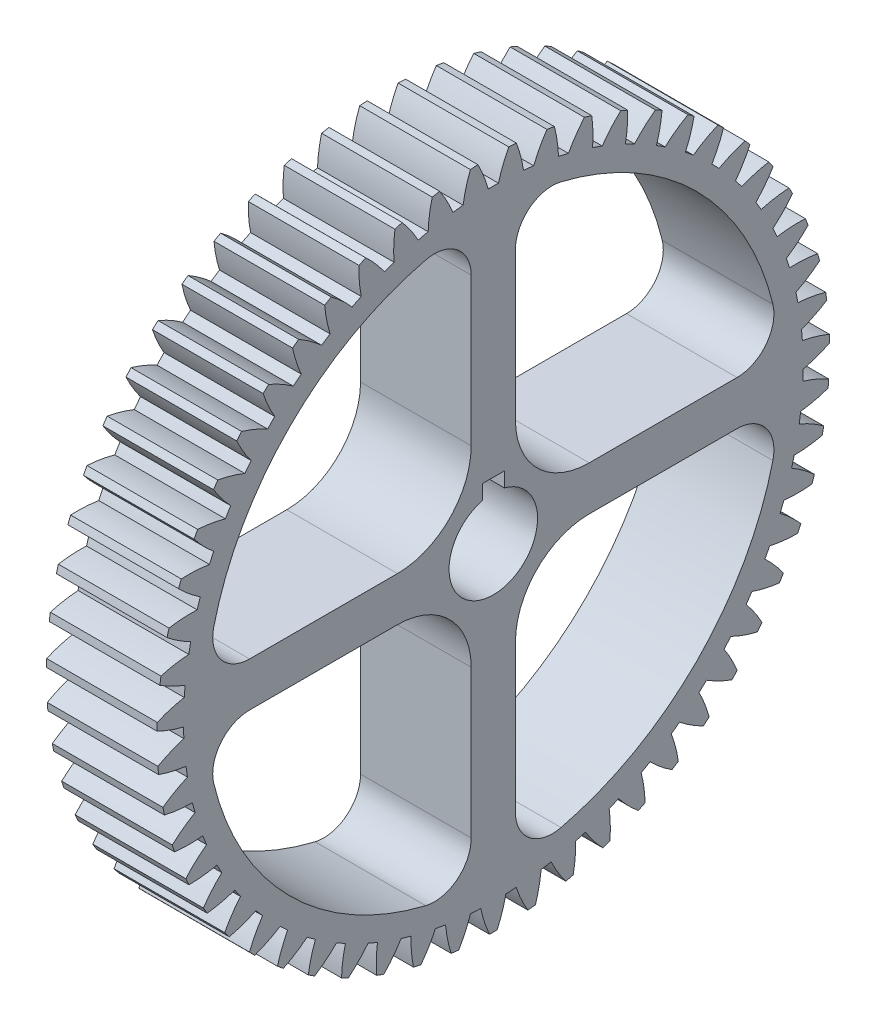
SolidWorks part; units mm, degrees
ref_plane "Plane1" through (0, 0, 0) normal (0, 0, 1) x (1, 0, 0)
ref_plane "Plane2" through (0, 0, 0) normal (0, 1, 0) x (1, 0, 0)
ref_plane "Plane3" through (0, 0, 0) normal (1, 0, 0) x (0, 0, -1)
other "Configuration Table"
sketch "HoldingSke" plane through (0, 0, 0) normal (0, 1, 0) x (1, 0, 0)
  line L0 (0, 0) -> (0.717, -1.0239)
  line L1 (-15, 0) -> (100, 0) construction
  line L2 (0, 0) -> (-2.1039, 2.3779)
  line L3 (0, 0) -> (-11.863, 4.5341)
  line L4 (0, 0) -> (4.9534, 7.0742)
  line L5 (0, 0) -> (-46.8476, -17.4728)
  line L6 (0, 0) -> (-6.2172, -4.1948)
  line L7 (-2.1039, 2.3779) -> (8.6586, 51.2059)
  line L8 (-76.2, 54.61) -> (-76.1, 54.61)
  line L9 (-71.009, 38.7566) -> (-53.1078, 45.2721)
  line L10 (-76.2, 71.12) -> (104.1128, 71.12)
  line L11 (0, 0) -> (-7.5, 0)
  line L12 (-76.2, 101.6) -> (-76.17, 101.6)
  line L13 (24.9733, 27.94) -> (52.9518, 28.4284)
  line L14 (24.9733, 27.94) -> (24.9743, 27.94)
  line L15 (24.9733, 27.94) -> (100.4006, 29.5858)
  line L16 (-63.627, -0.8) -> (-12.827, -0.8)
  circle A0 centre (0, 0) radius 0.4
  circle A1 centre (0, 0) radius 20.999
  circle A2 centre (0, 0) radius 37.5
  circle A3 centre (0, 0) radius 0.4
  dimension "MHD" = 41.998
  dimension "Hub_dia" = 75
  dimension "Bore" = 0.8
  dimension "MBD" = 0.8
  dimension "Num_teeth" = 55
  dimension "Pitch" = 1.25
  dimension "Overall_len" = 50
  dimension "Show_teeth" = 55
  dimension "Thickness" = 7.5
  dimension "OAL" = 50.0001
  dimension "T_dim" = 0.1
  dimension "Ap" = 20
  dimension "H" = 19.05
  dimension "Pitch_radius" = 180.3128
  dimension "Width" = 7.5
  dimension "Backlash" = 0.03
  dimension "Addendum_fac" = 1
  dimension "Dedendum_fac" = 1.25
  dimension "Clearance_fac" = 0.25
  dimension "Dedendum_add" = 0.001
  dimension "Module" = 0.8
sketch "BasProSke" plane through (0, 0, 0) normal (0, 1, 0) x (1, 0, 0)
  line L0 (-10, 0) -> (60, 0) construction
  line L1 (0, 0) -> (0, 22.8)
  line L2 (0, 0) -> (7.5, 0)
  line L3 (7.5, 0) -> (7.5, 22.8)
  line L4 (7.5, 22.8) -> (0, 22.8)
  dimension "Thickness" = 7.5
  dimension "Diameter" = 45.6
revolve "Base-Revolve" add sketch "BasProSke" angle 360 about L0
sketch "TooCutSke" plane through (0, 0, 0) normal (1, 0, 0) x (0, 0, -1)
  line L1 (0, 0) -> (0, 107) construction
  line L2 (0, 0) -> (-0.6807, 21.9895) construction
  line L3 (0, 0) -> (-2.511, 43.9132) construction
  line L4 (-0.6807, 21.9895) -> (-1.2555, 21.9566) construction
  arc A0 (0.3461, 20.9961) -> (-0.3461, 20.9961) centre (0, 0) ccw
  arc A1 (1.0581, 22.8009) -> (-1.0581, 22.8009) centre (0, 0) ccw
  circle A2 centre (0, 0) radius 22 construction
  circle A3 centre (0, 0) radius 20.6732 construction
  arc A4 (-0.3461, 20.9961) -> (-1.0581, 22.8009) centre (-8.8382, 18.6887) ccw
  arc A5 (1.0581, 22.8009) -> (0.3461, 20.9961) centre (8.8382, 18.6887) ccw
  dimension "Root_dia" = 41.998
  dimension "Overcut_dia" = 45.6508
  dimension "Pitch_dia" = 44
  dimension "Base_dia" = 41.3465
  dimension "Flank_rad" = 8.8
  dimension "Half_ang" = 3.273
  dimension "Half_CT" = 0.5757
extrude "ToothCut" cut sketch "TooCutSke" along normal through all
fillet "Breaks" [suppressed] radius 0.016
fillet "RootFillets" [suppressed] radius 0.201
pattern_circular "TeethCuts" count 55 every 6.545 about axis through (-10, 0, 0) along (1, 0, 0) of "ToothCut", "RootFillets", "Breaks"
sketch "HubNeaOneSke" plane through (0, 0, 0) normal (-1, 0, 0) x (0, 0, 1)
  circle A0 centre (0, 0) radius 20.999
  dimension "Diameter" = 41.998
extrude "HubNearOne" [suppressed] add sketch "HubNeaOneSke" along normal blind 42.5001
sketch "HubNeaBotSke" plane through (0, 0, 0) normal (-1, 0, 0) x (0, 0, 1)
  circle A0 centre (0, 0) radius 20.999
  dimension "Diameter" = 41.998
extrude "HubNearBoth" [suppressed] add sketch "HubNeaBotSke" along normal blind 21.25
ref_plane "FarPln" through (7.5, 0, 0) normal (1, 0, 0) x (0, 0, -1)
sketch "HubFarSke" plane through (7.5, 0, 0) normal (1, 0, 0) x (0, 0, -1)
  circle A0 centre (0, 0) radius 20.999
  dimension "Diameter" = 41.998
extrude "HubFar" [suppressed] add sketch "HubFarSke" along normal blind 21.25
sketch "BorSke" plane through (0, 0, 0) normal (1, 0, 0) x (0, 0, -1)
  circle A0 centre (0, 0) radius 0.4
  dimension "Diameter" = 0.8
extrude "Bore" cut sketch "BorSke" along normal mid plane 100.0001
sketch "KeySke" plane through (0, 0, 0) normal (1, 0, 0) x (0, 0, -1)
  line L0 (-0.05, 0) -> (-0.05, 0.5)
  line L1 (-0.05, 0.5) -> (0.05, 0.5)
  line L2 (0.05, 0.5) -> (0.05, 0)
  line L3 (0, 0) -> (0, 34) construction
  line L4 (-0.05, 0) -> (0.05, 0)
  dimension "Offset" = 0.5
  dimension "Width" = 0.1
extrude "Keyway" [suppressed] cut sketch "KeySke" along normal mid plane 100.0001
pattern_circular "Keyway2" [suppressed] count 2 every 90 about axis through (-10, 0, 0) along (1, 0, 0)
sketch "Sketch1" plane through (7.5, 0, 0) normal (1, 0, 0) x (0, 0, -1)
  circle A0 centre (0, 0) radius 0.4 construction
  circle A1 centre (0, 0) radius 0.4
extrude "Boss-Extrude1" add sketch "Sketch1" against normal up to surface (7.5 mm away) up to face at (0, 0, -0.4)
sketch "Sketch2" plane through (7.5, 0, 0) normal (1, 0, 0) x (0, 0, -1)
  line L0 (-15.0591, 14.635) -> (-13.9834, 13.5896) construction
  circle A0 centre (0, 0) radius 19.499
  arc A1 (-14.8158, 14.8812) -> (-15.2982, 14.3848) centre (0, 0) ccw construction
  dimension "D1" = 1.5
extrude "Cut-Extrude1" cut sketch "Sketch2" against normal blind 10
sketch "Sketch3" plane through (7.5, 0, 0) normal (1, 0, 0) x (0, 0, -1)
  line L0 (0, 19.499) -> (0, -19.499) construction
  line L5 (-19.499, 0) -> (19.499, 0) construction
  line L6 (-19.4412, -1.5) -> (-6.5, -1.5)
  line L7 (-19.4412, 1.5) -> (-6.5, 1.5)
  line L8 (-19.499, 1.5) -> (19.499, 1.5) construction
  line L9 (-19.499, -1.5) -> (19.499, -1.5) construction
  line L10 (-1.5, 19.4412) -> (-1.5, 6.5)
  line L11 (1.5, 19.4412) -> (1.5, 6.5)
  line L12 (-1.5, 19.499) -> (-1.5, -19.499) construction
  line L13 (1.5, 19.499) -> (1.5, -19.499) construction
  line L14 (-1.5, -6.5) -> (-1.5, -19.4412)
  line L15 (6.5, 1.5) -> (19.4412, 1.5)
  line L16 (1.5, -6.5) -> (1.5, -19.4412)
  line L17 (6.5, -1.5) -> (19.4412, -1.5)
  circle A0 centre (0, 0) radius 19.499 construction
  arc A1 (19.4412, -1.5) -> (19.4412, 1.5) centre (0, 0) ccw
  arc A2 (-1.5, -19.4412) -> (1.5, -19.4412) centre (0, 0) ccw
  arc A3 (-19.4412, 1.5) -> (-19.4412, -1.5) centre (0, 0) ccw
  arc A4 (1.5, 19.4412) -> (-1.5, 19.4412) centre (0, 0) ccw
  arc A5 (-6.5, 1.5) -> (-1.5, 6.5) centre (-6.5, 6.5) ccw
  arc A6 (1.5, 6.5) -> (6.5, 1.5) centre (6.5, 6.5) ccw
  arc A7 (6.5, -1.5) -> (1.5, -6.5) centre (6.5, -6.5) ccw
  arc A8 (-1.5, -6.5) -> (-6.5, -1.5) centre (-6.5, -6.5) ccw
  point P0 (0, 0)
  point P8 (0, 0)
  point P11 (0, 0)
  point P37 (1.5, -1.5)
  dimension "D5" = 5
  dimension "D1" = 1.5
  dimension "D2" = 1.5
  dimension "D3" = 1.5
  dimension "D4" = 1.5
extrude "Boss-Extrude2" add sketch "Sketch3" against normal up to surface (7.5 mm away)
fillet "Fillet1" radius 2.5 8 edges at (3.75, 1.5, 19.4412) (3.75, -1.5, 19.4412) (3.75, -19.4412, -1.5) (3.75, -19.4412, 1.5) (3.75, 19.4412, 1.5) (3.75, 19.4412, -1.5) (3.75, 1.5, -19.4412) (3.75, -1.5, -19.4412)
sketch "Sketch4" plane through (0, 0, 0) normal (-1, 0, 0) x (0, 0, 1)
  line L0 (0, 0) -> (0, 50000) construction
  line L1 (-0.75, 2.9047) -> (-0.75, 3.9047)
  line L2 (0.75, 2.9047) -> (0.75, 3.9047)
  line L3 (-0.75, 3.9047) -> (0.75, 3.9047)
  arc A0 (-0.75, 2.9047) -> (0.75, 2.9047) centre (0, 0) ccw
  point P7 (-0.75, 3.4047)
  dimension "D1" = 6
  dimension "D2" = 1
  dimension "D3" = 1.5
extrude "Cut-Extrude2" cut sketch "Sketch4" against normal through all
equation "' \"Module@HoldingSke\" = 6.35"
equation "' \"Num_teeth@HoldingSke\" = 12"
equation "' \"Ap@HoldingSke\" =  20"
equation "' \"Ap@HoldingSke\" = 20"
equation "' \"Width@HoldingSke\" = 0.5 * 25.4"
equation "' \"Hub_dia@HoldingSke\"= 1 * 25.4"
equation "' \"Hub_dia@HoldingSke\" = 1 * 25.4"
equation "' \"Overall_len@HoldingSke\" = 1.0 * 25.4"
equation "' \"Bore@HoldingSke\" = 0.75 * 25.4"
equation "' \"T_dim@HoldingSke\" = 0.1 * 25.4"
equation "' \"Width@KeySke\" = 0.25 * 25.4"
equation "' \"Show_teeth@HoldingSke\" = 13"
equation "' \"Backlash@HoldingSke\" = 0.009 * 25.4"
equation "' \"Addendum_fac@HoldingSke\" = 1.0"
equation "' \"Dedendum_fac@HoldingSke\" = 1.25"
equation "' \"Dedendum_add@HoldingSke\" = 0.00005 * 25.4"
equation "' \"Clearance_fac@HoldingSke\" = 0.25"
equation "\"Pitch@HoldingSke\" = 1 / \"Module@HoldingSke\""
equation "\"Overcut_dia@TooCutSke\" = (\"Num_teeth@HoldingSke\" + 2 * \"Addendum_fac@HoldingSke\") / \"Pitch@HoldingSke\" + 0.002 * 25.4"
equation "\"Pitch_dia@TooCutSke\" = \"Num_teeth@HoldingSke\" / \"Pitch@HoldingSke\""
equation "\"Base_dia@TooCutSke\" = \"Num_teeth@HoldingSke\" / \"Pitch@HoldingSke\" * cos((\"Ap@HoldingSke\"  * 3.14159265 / 180))"
equation "\"Root_dia@TooCutSke\" = (\"Num_teeth@HoldingSke\" + 2) / \"Pitch@HoldingSke\" - 2 * (\"Addendum_fac@HoldingSke\" + \"Dedendum_fac@HoldingSke\") / \"Pitch@HoldingSke\" - \"Dedendum_add@HoldingSke\" * 2"
equation "\"Half_ang@TooCutSke\" = 180 / \"Num_teeth@HoldingSke\""
equation "\"Half_CT@TooCutSke\" = \"Num_teeth@HoldingSke\" / \"Pitch@HoldingSke\" * sin((3.14159265 / 2 / \"Num_teeth@HoldingSke\")) / 2 - 7 * \"Backlash@HoldingSke\" / 4"
equation "\"Flank_rad@TooCutSke\" = \"Num_teeth@HoldingSke\" / \"Pitch@HoldingSke\" / 5"
equation "\"Radius@RootFillets\" = \"Clearance_fac@HoldingSke\" / \"Pitch@HoldingSke\" + \"Dedendum_add@HoldingSke\""
equation "\"Break_rad@Breaks\" = 0.02 / \"Pitch@HoldingSke\""
equation "\"Thickness@HoldingSke\" = \"Width@HoldingSke\""
equation "\"OAL@HoldingSke\" = \"Thickness@HoldingSke\""
equation "\"MHD@HoldingSke\" = (\"Num_teeth@HoldingSke\" + 2) / \"Pitch@HoldingSke\" - 2 * (\"Addendum_fac@HoldingSke\" + \"Dedendum_fac@HoldingSke\")  / \"Pitch@HoldingSke\" - \"Dedendum_add@HoldingSke\" * 2"
equation "\"MBD@HoldingSke\" = (\"Num_teeth@HoldingSke\" + 2) / \"Pitch@HoldingSke\" - 2 * (\"Addendum_fac@HoldingSke\" + \"Dedendum_fac@HoldingSke\")  / \"Pitch@HoldingSke\" - \"Dedendum_add@HoldingSke\" * 2 - 0.002 * 25.4"
equation "\"MHD@HoldingSke\" = ((sgn( \"MHD@HoldingSke\" - \"Hub_dia@HoldingSke\" )-1)*( \"MHD@HoldingSke\" - \"Hub_dia@HoldingSke\" ))/-2+ \"Hub_dia@HoldingSke\""
equation "\"MBD@HoldingSke\" = ((sgn( \"MBD@HoldingSke\" - \"Bore@HoldingSke\" )-1)*( \"MBD@HoldingSke\" - \"Bore@HoldingSke\" ))/-2+ \"Bore@HoldingSke\""
equation "\"OAL@HoldingSke\" = ((sgn( \"OAL@HoldingSke\" - \"Overall_len@HoldingSke\" )+1)*( \"OAL@HoldingSke\" - \"Overall_len@HoldingSke\" ))/2 + \"Overall_len@HoldingSke\" + 0.000002 * 25.4"
equation "\"Num_teeth@TeethCuts\" = int( \"Show_teeth@HoldingSke\" ) + 1"
equation "\"Num_teeth@TeethCuts\" = ((sgn( \"Num_teeth@TeethCuts\" - \"Num_teeth@HoldingSke\" )-1)*( \"Num_teeth@TeethCuts\" - \"Num_teeth@HoldingSke\" ))/-2+ \"Num_teeth@HoldingSke\""
equation "\"Num_teeth@TeethCuts\" = ((sgn( \"Num_teeth@TeethCuts\" - 2.0)+1)*( \"Num_teeth@TeethCuts\" - 2.0))/2 +2.0"
equation "\"Angle@TeethCuts\" = 360.0 / \"Num_teeth@HoldingSke\""
equation "\"Diameter@BasProSke\" = (\"Num_teeth@HoldingSke\" + 2 * \"Addendum_fac@HoldingSke\") / \"Pitch@HoldingSke\""
equation "\"Thickness@BasProSke\"  = \"Thickness@HoldingSke\""
equation "' \"Fillet_rad@BasProSke\" =  \"Thickness@HoldingSke\" * 0.05"
equation "' \"Fillet_rad@BasProSke\" = \"Thickness@HoldingSke\" * 0.05"
equation "\"MHD@HoldingSke\" = ((sgn( \"MHD@HoldingSke\" - \"Root_dia@TooCutSke\" )-1)*( \"MHD@HoldingSke\" - \"Root_dia@TooCutSke\" ))/-2+ \"Root_dia@TooCutSke\""
equation "\"Diameter@HubNeaOneSke\" = \"MHD@HoldingSke\""
equation "\"Length@HubNearOne\" = \"OAL@HoldingSke\" - \"Thickness@BasProSke\""
equation "\"Diameter@HubNeaBotSke\" = \"MHD@HoldingSke\""
equation "\"Length@HubNearBoth\" = ( \"OAL@HoldingSke\" - \"Thickness@BasProSke\" ) / 2.0"
equation "\"Thickness@FarPln\" = \"Thickness@BasProSke\""
equation "\"Diameter@HubFarSke\" = \"MHD@HoldingSke\""
equation "\"Length@HubFar\" = ( \"OAL@HoldingSke\" - \"Thickness@BasProSke\" ) / 2.0"
equation "\"Diameter@BorSke\" = \"MBD@HoldingSke\""
equation "\"D1@Bore\" = \"OAL@HoldingSke\" * 2.0"
equation "\"D1@Keyway\" = \"OAL@HoldingSke\" * 2.0"
equation "\"Offset@KeySke\" = \"T_dim@HoldingSke\" + \"MBD@HoldingSke\" / 2.0"
